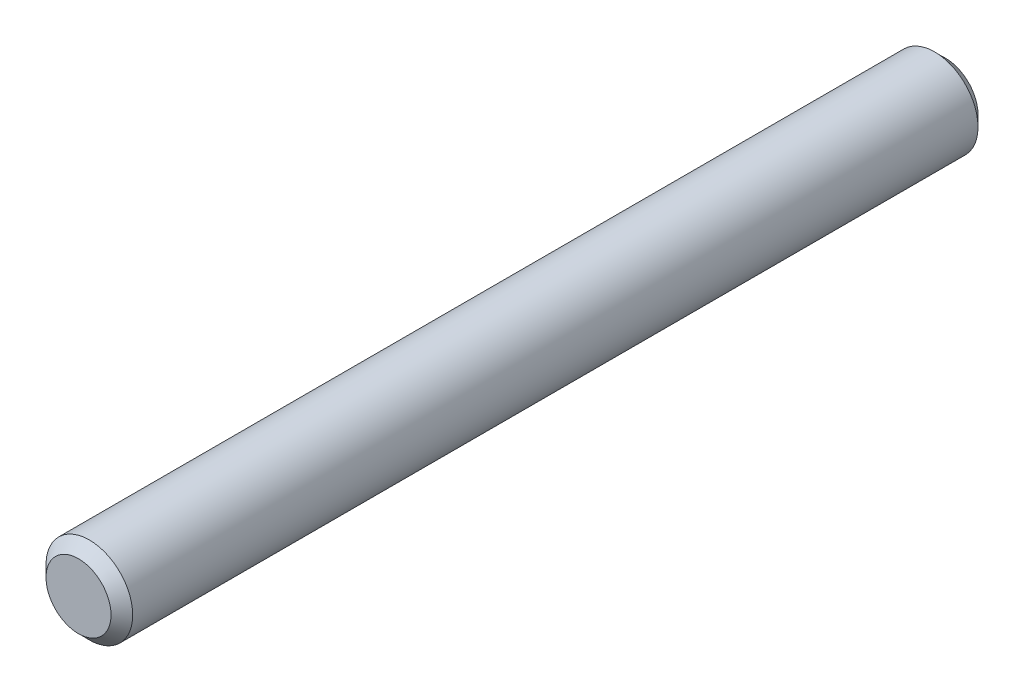
SolidWorks part; units mm, degrees
ref_plane "Face" through (0, 0, 0) normal (0, 0, 1) x (1, 0, 0)
ref_plane "Dessus" through (0, 0, 0) normal (0, 1, 0) x (1, 0, 0)
ref_plane "Droite" through (0, 0, 0) normal (1, 0, 0) x (0, 0, -1)
sketch "Esquisse2" plane through (0, 0, 0) normal (0, 0, 1) x (1, 0, 0)
  circle A0 centre (0, 0) radius 4
  dimension "D1" = 8
extrude "Extrusion1" add sketch "Esquisse2" along normal blind 80
chamfer "Chanfrein1" distance 1 angle 45 2 edges at (4, 0, 0) (4, 0, 80)
